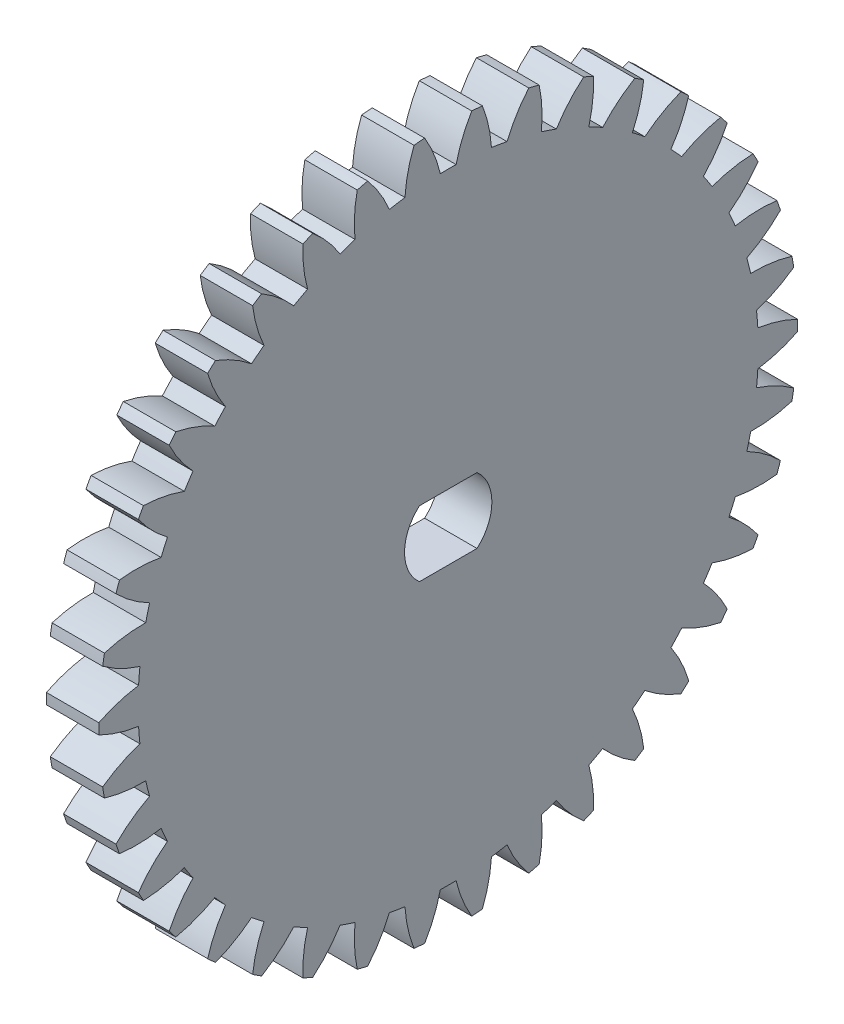
SolidWorks part; units mm, degrees
ref_plane "Plane1" through (0, 0, 0) normal (0, 0, 1) x (1, 0, 0)
ref_plane "Plane2" through (0, 0, 0) normal (0, 1, 0) x (1, 0, 0)
ref_plane "Plane3" through (0, 0, 0) normal (1, 0, 0) x (0, 0, -1)
sketch "HoldingSke" plane through (0, 0, 0) normal (0, 1, 0) x (1, 0, 0)
  line L0 (0, 0) -> (0.788, -0.6157)
  line L1 (-15, 0) -> (100, 0) construction
  line L2 (0, 0) -> (-2.1039, 2.3779)
  line L3 (0, 0) -> (-11.863, 4.5341)
  line L4 (0, 0) -> (6.8053, 5.3169)
  line L5 (0, 0) -> (-46.8476, -17.4728)
  line L6 (0, 0) -> (-2.4869, -1.6779)
  line L7 (-2.1039, 2.3779) -> (8.6586, 51.2059)
  line L8 (-76.2, 54.61) -> (-75.3, 54.61)
  line L9 (-71.009, 38.7566) -> (-53.1078, 45.2721)
  line L10 (-76.2, 71.12) -> (104.1128, 71.12)
  line L11 (0, 0) -> (-3, 0)
  line L12 (-76.2, 101.6) -> (-76.162, 101.6)
  line L13 (24.9733, 27.94) -> (52.9518, 28.4284)
  line L14 (24.9733, 27.94) -> (24.9743, 27.94)
  line L15 (24.9733, 27.94) -> (100.4006, 29.5858)
  line L16 (-63.627, -1) -> (-12.827, -1)
  circle A0 centre (0, 0) radius 2.5
  circle A1 centre (0, 0) radius 17.749
  circle A2 centre (0, 0) radius 37.5
  circle A3 centre (0, 0) radius 2.5
  dimension "MHD" = 35.498
  dimension "Hub_dia" = 75
  dimension "Bore" = 5
  dimension "MBD" = 5
  dimension "Num_teeth" = 38
  dimension "Pitch" = 1
  dimension "Overall_len" = 50
  dimension "Show_teeth" = 38
  dimension "Thickness" = 3
  dimension "OAL" = 50.0001
  dimension "T_dim" = 0.9
  dimension "Ap" = 20
  dimension "H" = 19.05
  dimension "Pitch_radius" = 180.3128
  dimension "Width" = 3
  dimension "Backlash" = 0.038
  dimension "Addendum_fac" = 1
  dimension "Dedendum_fac" = 1.25
  dimension "Clearance_fac" = 0.25
  dimension "Dedendum_add" = 0.001
  dimension "Module" = 1
sketch "BasProSke" plane through (0, 0, 0) normal (0, 1, 0) x (1, 0, 0)
  line L0 (-10, 0) -> (60, 0) construction
  line L1 (0, 0) -> (0, 20)
  line L2 (0, 0) -> (3, 0)
  line L3 (3, 0) -> (3, 20)
  line L4 (3, 20) -> (0, 20)
  dimension "Thickness" = 3
  dimension "Diameter" = 40
revolve "Base-Revolve" add sketch "BasProSke" angle 360 about L0
sketch "TooCutSke" plane through (0, 0, 0) normal (1, 0, 0) x (0, 0, -1)
  line L1 (0, 0) -> (0, 107) construction
  line L2 (0, 0) -> (-0.8517, 18.9809) construction
  line L3 (0, 0) -> (-3.1358, 37.8431) construction
  line L4 (-0.8517, 18.9809) -> (-1.5679, 18.9216) construction
  arc A0 (0.4515, 17.7433) -> (-0.4515, 17.7433) centre (0, 0) ccw
  arc A1 (1.3614, 19.9791) -> (-1.3614, 19.9791) centre (0, 0) ccw
  circle A2 centre (0, 0) radius 19 construction
  circle A3 centre (0, 0) radius 17.8542 construction
  arc A4 (-0.4515, 17.7433) -> (-1.3614, 19.9791) centre (-7.8565, 16.0327) ccw
  arc A5 (1.3614, 19.9791) -> (0.4515, 17.7433) centre (7.8565, 16.0327) ccw
  dimension "Root_dia" = 35.498
  dimension "Overcut_dia" = 40.0508
  dimension "Pitch_dia" = 38
  dimension "Base_dia" = 35.7083
  dimension "Flank_rad" = 7.6
  dimension "Half_ang" = 4.737
  dimension "Half_CT" = 0.7187
extrude "ToothCut" cut sketch "TooCutSke" along normal through all
fillet "Breaks" [suppressed] radius 0.02
fillet "RootFillets" [suppressed] radius 0.251
pattern_circular "TeethCuts" count 38 every 9.474 about axis through (-10, 0, 0) along (1, 0, 0) of "ToothCut", "RootFillets", "Breaks"
sketch "HubNeaOneSke" plane through (0, 0, 0) normal (-1, 0, 0) x (0, 0, 1)
  circle A0 centre (0, 0) radius 17.749
  dimension "Diameter" = 35.498
extrude "HubNearOne" [suppressed] add sketch "HubNeaOneSke" along normal blind 47.0001
sketch "HubNeaBotSke" plane through (0, 0, 0) normal (-1, 0, 0) x (0, 0, 1)
  circle A0 centre (0, 0) radius 17.749
  dimension "Diameter" = 35.498
extrude "HubNearBoth" [suppressed] add sketch "HubNeaBotSke" along normal blind 23.5
ref_plane "FarPln" through (3, 0, 0) normal (1, 0, 0) x (0, 0, -1)
sketch "HubFarSke" plane through (3, 0, 0) normal (1, 0, 0) x (0, 0, -1)
  circle A0 centre (0, 0) radius 17.749
  dimension "Diameter" = 35.498
extrude "HubFar" [suppressed] add sketch "HubFarSke" along normal blind 23.5
sketch "BorSke" plane through (0, 0, 0) normal (1, 0, 0) x (0, 0, -1)
  circle A0 centre (0, 0) radius 2.5
  dimension "Diameter" = 5
extrude "Bore" cut sketch "BorSke" along normal mid plane 100.0001
sketch "KeySke" plane through (0, 0, 0) normal (1, 0, 0) x (0, 0, -1)
  line L0 (-1, 0) -> (-1, 3.4)
  line L1 (-1, 3.4) -> (1, 3.4)
  line L2 (1, 3.4) -> (1, 0)
  line L3 (0, 0) -> (0, 34) construction
  line L4 (-1, 0) -> (1, 0)
  dimension "Offset" = 3.4
  dimension "Width" = 2
extrude "Keyway" [suppressed] cut sketch "KeySke" along normal mid plane 100.0001
pattern_circular "Keyway2" [suppressed] count 2 every 90 about axis through (-10, 0, 0) along (1, 0, 0)
sketch "Szkic1" plane through (0, 0, 0) normal (-1, 0, 0) x (0, 0, 1)
  line L0 (0, -2.5) -> (0, -1.88) construction
  line L1 (-2.7472, 1.88) -> (2.7528, 1.88)
  line L2 (-2.7472, 1.88) -> (-2.7472, -1.88)
  line L3 (-2.7472, -1.88) -> (2.7528, -1.88)
  line L4 (2.7528, 1.88) -> (2.7528, -1.88)
  line L5 (0, 2.5) -> (0, 1.88) construction
  line L7 (-4.3363, 3.2001) -> (4.4895, 3.2001)
  line L8 (-4.3363, 3.2001) -> (-4.3363, -3.137)
  line L9 (-4.3363, -3.137) -> (4.4895, -3.137)
  line L10 (4.4895, 3.2001) -> (4.4895, -3.137)
  circle A1 centre (0, 0) radius 2.5 construction
extrude "Dodanie-wyciągnięcie1" add sketch "Szkic1" against normal blind 3
equation "' \"Module@HoldingSke\" = 6.35"
equation "' \"Num_teeth@HoldingSke\" = 12"
equation "' \"Ap@HoldingSke\" =  20"
equation "' \"Ap@HoldingSke\" = 20"
equation "' \"Width@HoldingSke\" = 0.5 * 25.4"
equation "' \"Hub_dia@HoldingSke\"= 1 * 25.4"
equation "' \"Hub_dia@HoldingSke\" = 1 * 25.4"
equation "' \"Overall_len@HoldingSke\" = 1.0 * 25.4"
equation "' \"Bore@HoldingSke\" = 0.75 * 25.4"
equation "' \"T_dim@HoldingSke\" = 0.1 * 25.4"
equation "' \"Width@KeySke\" = 0.25 * 25.4"
equation "' \"Show_teeth@HoldingSke\" = 13"
equation "' \"Backlash@HoldingSke\" = 0.009 * 25.4"
equation "' \"Addendum_fac@HoldingSke\" = 1.0"
equation "' \"Dedendum_fac@HoldingSke\" = 1.25"
equation "' \"Dedendum_add@HoldingSke\" = 0.00005 * 25.4"
equation "' \"Clearance_fac@HoldingSke\" = 0.25"
equation "\"Pitch@HoldingSke\" = 1 / \"Module@HoldingSke\""
equation "\"Overcut_dia@TooCutSke\" = (\"Num_teeth@HoldingSke\" + 2 * \"Addendum_fac@HoldingSke\") / \"Pitch@HoldingSke\" + 0.002 * 25.4"
equation "\"Pitch_dia@TooCutSke\" = \"Num_teeth@HoldingSke\" / \"Pitch@HoldingSke\""
equation "\"Base_dia@TooCutSke\" = \"Num_teeth@HoldingSke\" / \"Pitch@HoldingSke\" * cos((\"Ap@HoldingSke\"  * 3.14159265 / 180))"
equation "\"Root_dia@TooCutSke\" = (\"Num_teeth@HoldingSke\" + 2) / \"Pitch@HoldingSke\" - 2 * (\"Addendum_fac@HoldingSke\" + \"Dedendum_fac@HoldingSke\") / \"Pitch@HoldingSke\" - \"Dedendum_add@HoldingSke\" * 2"
equation "\"Half_ang@TooCutSke\" = 180 / \"Num_teeth@HoldingSke\""
equation "\"Half_CT@TooCutSke\" = \"Num_teeth@HoldingSke\" / \"Pitch@HoldingSke\" * sin((3.14159265 / 2 / \"Num_teeth@HoldingSke\")) / 2 - 7 * \"Backlash@HoldingSke\" / 4"
equation "\"Flank_rad@TooCutSke\" = \"Num_teeth@HoldingSke\" / \"Pitch@HoldingSke\" / 5"
equation "\"Radius@RootFillets\" = \"Clearance_fac@HoldingSke\" / \"Pitch@HoldingSke\" + \"Dedendum_add@HoldingSke\""
equation "\"Break_rad@Breaks\" = 0.02 / \"Pitch@HoldingSke\""
equation "\"Thickness@HoldingSke\" = \"Width@HoldingSke\""
equation "\"OAL@HoldingSke\" = \"Thickness@HoldingSke\""
equation "\"MHD@HoldingSke\" = (\"Num_teeth@HoldingSke\" + 2) / \"Pitch@HoldingSke\" - 2 * (\"Addendum_fac@HoldingSke\" + \"Dedendum_fac@HoldingSke\")  / \"Pitch@HoldingSke\" - \"Dedendum_add@HoldingSke\" * 2"
equation "\"MBD@HoldingSke\" = (\"Num_teeth@HoldingSke\" + 2) / \"Pitch@HoldingSke\" - 2 * (\"Addendum_fac@HoldingSke\" + \"Dedendum_fac@HoldingSke\")  / \"Pitch@HoldingSke\" - \"Dedendum_add@HoldingSke\" * 2 - 0.002 * 25.4"
equation "\"MHD@HoldingSke\" = ((sgn( \"MHD@HoldingSke\" - \"Hub_dia@HoldingSke\" )-1)*( \"MHD@HoldingSke\" - \"Hub_dia@HoldingSke\" ))/-2+ \"Hub_dia@HoldingSke\""
equation "\"MBD@HoldingSke\" = ((sgn( \"MBD@HoldingSke\" - \"Bore@HoldingSke\" )-1)*( \"MBD@HoldingSke\" - \"Bore@HoldingSke\" ))/-2+ \"Bore@HoldingSke\""
equation "\"OAL@HoldingSke\" = ((sgn( \"OAL@HoldingSke\" - \"Overall_len@HoldingSke\" )+1)*( \"OAL@HoldingSke\" - \"Overall_len@HoldingSke\" ))/2 + \"Overall_len@HoldingSke\" + 0.000002 * 25.4"
equation "\"Num_teeth@TeethCuts\" = int( \"Show_teeth@HoldingSke\" ) + 1"
equation "\"Num_teeth@TeethCuts\" = ((sgn( \"Num_teeth@TeethCuts\" - \"Num_teeth@HoldingSke\" )-1)*( \"Num_teeth@TeethCuts\" - \"Num_teeth@HoldingSke\" ))/-2+ \"Num_teeth@HoldingSke\""
equation "\"Num_teeth@TeethCuts\" = ((sgn( \"Num_teeth@TeethCuts\" - 2.0)+1)*( \"Num_teeth@TeethCuts\" - 2.0))/2 +2.0"
equation "\"Angle@TeethCuts\" = 360.0 / \"Num_teeth@HoldingSke\""
equation "\"Diameter@BasProSke\" = (\"Num_teeth@HoldingSke\" + 2 * \"Addendum_fac@HoldingSke\") / \"Pitch@HoldingSke\""
equation "\"Thickness@BasProSke\"  = \"Thickness@HoldingSke\""
equation "' \"Fillet_rad@BasProSke\" =  \"Thickness@HoldingSke\" * 0.05"
equation "' \"Fillet_rad@BasProSke\" = \"Thickness@HoldingSke\" * 0.05"
equation "\"MHD@HoldingSke\" = ((sgn( \"MHD@HoldingSke\" - \"Root_dia@TooCutSke\" )-1)*( \"MHD@HoldingSke\" - \"Root_dia@TooCutSke\" ))/-2+ \"Root_dia@TooCutSke\""
equation "\"Diameter@HubNeaOneSke\" = \"MHD@HoldingSke\""
equation "\"Length@HubNearOne\" = \"OAL@HoldingSke\" - \"Thickness@BasProSke\""
equation "\"Diameter@HubNeaBotSke\" = \"MHD@HoldingSke\""
equation "\"Length@HubNearBoth\" = ( \"OAL@HoldingSke\" - \"Thickness@BasProSke\" ) / 2.0"
equation "\"Thickness@FarPln\" = \"Thickness@BasProSke\""
equation "\"Diameter@HubFarSke\" = \"MHD@HoldingSke\""
equation "\"Length@HubFar\" = ( \"OAL@HoldingSke\" - \"Thickness@BasProSke\" ) / 2.0"
equation "\"Diameter@BorSke\" = \"MBD@HoldingSke\""
equation "\"D1@Bore\" = \"OAL@HoldingSke\" * 2.0"
equation "\"D1@Keyway\" = \"OAL@HoldingSke\" * 2.0"
equation "\"Offset@KeySke\" = \"T_dim@HoldingSke\" + \"MBD@HoldingSke\" / 2.0"
